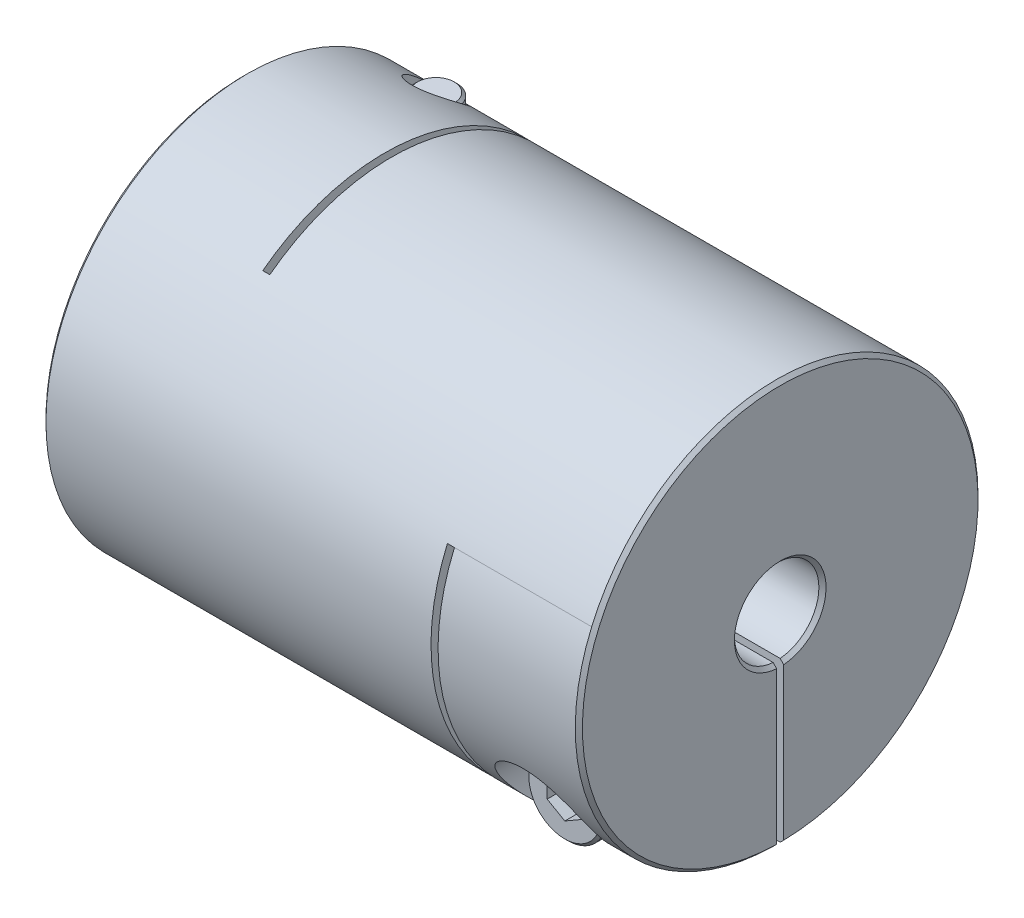
SolidWorks part; units mm, degrees
ref_plane "Front Plane" through (0, 0, 0) normal (0, 0, 1) x (1, 0, 0)
ref_plane "Top Plane" through (0, 0, 0) normal (0, 1, 0) x (1, 0, 0)
ref_plane "Right Plane" through (0, 0, 0) normal (1, 0, 0) x (0, 0, -1)
sketch "Sketch1" plane through (0, 0, 0) normal (1, 0, 0) x (0, 0, -1)
  circle A0 centre (0, 0) radius 14.3
  dimension "dim D" = 28.6
extrude "Boss-Extrude1" add sketch "Sketch1" along normal mid plane 38.1
sketch "Sketch2" plane through (19.05, 0, 0) normal (1, 0, 0) x (0, 0, -1)
  circle A0 centre (0, 0) radius 3
  dimension "dim D1" = 6
extrude "Cut-Extrude1" cut sketch "Sketch2" against normal through all
chamfer "Chamfer1" distance 0.254 angle 45 4 edges at (-19.05, 0, -3) (-19.05, 0, -14.3) (19.05, 0, -14.3) (19.05, 0, -3)
ref_plane "Plane2" through (0, -14.3, 0) normal (0, -1, 0) x (1, 0, 0)
ref_plane "L1" through (-14.05, 0, 0) normal (-1, 0, 0) x (0, 0, 1)
sketch "Sketch4" plane through (0, -14.3, 0) normal (0, -1, 0) x (1, 0, 0)
  line L0 (-18.796, -14.3) -> (18.796, -14.3) construction
  line L1 (-9.05, -14.3) -> (-8.55, -14.3)
  line L2 (-9.05, -14.3) -> (-9.05, 8.65)
  line L3 (-9.05, 8.65) -> (-8.55, 8.65)
  line L4 (-8.55, -14.3) -> (-8.55, 8.65)
  line L5 (-9.05, 3) -> (-9.05, 14.3) construction
  line L6 (18.796, 3) -> (-18.796, 3) construction
  line L7 (18.796, 14.3) -> (-18.796, 14.3) construction
  line L10 (-9.05, 8.65) -> (-19.05, 8.65) construction
  line L11 (-19.05, 14.046) -> (-19.05, -14.046) construction
  line L12 (-14.05, 10.2256) -> (-14.05, -10.2256) construction
  point P16 (-14.05, 8.65)
  dimension "D1" = 0.5
extrude "Cut-Extrude2" cut sketch "Sketch4" against normal through all
ref_plane "Plane4" through (0, 0, -14.3) normal (0, 0, -1) x (-1, 0, 0)
sketch "Sketch7" plane through (0, 0, -14.3) normal (0, 0, -1) x (-1, 0, 0)
  line L1 (-8.55, -14.3) -> (-9.05, -14.3)
  line L2 (-9.05, -14.3) -> (-9.05, 5.65)
  line L3 (-9.05, 5.65) -> (-8.55, 5.65)
  line L4 (-8.55, -14.3) -> (-8.55, 5.65)
  line L5 (19.05, 8.6487) -> (14.05, 8.6487) construction
  line L7 (-10.505, -14.3) -> (10.505, -14.3) construction
  line L8 (-18.796, -3) -> (8.55, -3) construction
  line L9 (19.05, -14.046) -> (19.05, 14.046) construction
  line L10 (-18.796, -3) -> (8.55, -3) construction
  line L11 (8.55, 11.3872) -> (9.05, 11.3872) construction
  line L12 (-9.05, 5.65) -> (-9.05, -14.3) construction
  line L14 (-18.796, -3) -> (8.55, -3) construction
  line L16 (-18.796, -3) -> (8.55, -3) construction
  line L17 (9.05, -14.3) -> (18.796, -14.3) construction
  line L18 (14.05, -10.2256) -> (14.05, 10.2256) construction
  line L19 (-18.796, -14.3) -> (-18.796, 14.3) construction
  line L20 (-19.05, 5.65) -> (-14.05, 5.65) construction
  line L21 (-19.05, 14.046) -> (-19.05, -14.046) construction
  line L22 (-14.05, 5.65) -> (-9.05, 5.65) construction
  line L23 (-18.796, -14.3) -> (-18.796, 14.3) construction
  line L24 (-18.796, -3) -> (-18.796, 14.3) construction
  line L25 (-18.796, -3) -> (8.55, -3) construction
  point P23 (-9.05, 5.65)
  point P33 (-18.796, 5.65)
extrude "Cut-Extrude3" cut sketch "Sketch7" against normal through all
sketch "Sketch8" plane through (0, 0, 0) normal (0, 1, 0) x (1, 0, 0)
  line L0 (-9.05, -8.65) -> (-9.05, 14.3) construction
  line L1 (-19.05, 14.3) -> (-9.05, 14.3)
  line L2 (-19.05, 14.3) -> (-19.05, 0)
  line L3 (-19.05, 0) -> (-9.05, 0)
  line L4 (-9.05, 14.3) -> (-9.05, 0)
  line L5 (10.505, 14.3) -> (-10.505, 14.3) construction
  line L6 (-19.05, 14.046) -> (-19.05, -14.046) construction
extrude "Cut-Extrude5" cut sketch "Sketch8" against normal mid plane 0.5
sketch "Sketch13" plane through (0, 0, 0) normal (0, 0, 1) x (1, 0, 0)
  line L0 (19.05, -14.046) -> (19.05, 14.046) construction
  line L1 (9.05, -14.3) -> (19.05, -14.3)
  line L2 (9.05, -14.3) -> (9.05, 0)
  line L3 (9.05, 0) -> (19.05, 0)
  line L4 (19.05, -14.3) -> (19.05, 0)
extrude "Cut-Extrude6" cut sketch "Sketch13" against normal mid plane 0.5
hole_wizard "CBORE for M3 SHCS1" positions "Sketch12" profile "Sketch11" counterbore size "M3" standard "Ansi Metric" end condition through all
sketch "Sketch12" plane through (0, -14.3, 0) normal (0, -1, 0) x (1, 0, 0)
  line L0 (-14.05, 10.2256) -> (-14.05, -10.2256) construction
  line L1 (-9.05, -2.9896) -> (-9.05, -14.2978) construction
  line L2 (-9.05, -2.9896) -> (-9.05, -14.2978)
  line L3 (-9.05, -8.6437) -> (-14.05, -8.6437) construction
  point P0 (-14.05, -8.6437)
sketch "Sketch11" plane through (-14.05, -14.3, -8.6437) normal (1, 0, 0) x (0, 0, -1)
  line L0 (0, 0) -> (0, 28.6)
  line L1 (0, 28.6) -> (1.7, 28.6)
  line L3 (1.7, 28.6) -> (1.7, 7)
  line L4 (1.7, 7) -> (3.25, 7)
  line L5 (3.25, 7) -> (3.25, 0)
  line L7 (3.25, 0) -> (0, 0)
  line L11 (0, -6.35) -> (0, 107.95) construction
  dimension "Thru Hole Dia." = 3.4
  dimension "Thru Hole Depth" = 28.6
  dimension "C'Bore Dia." = 6.5
  dimension "C'Bore Depth" = 7
ref_plane "Plane5" through (0, 0, 14.3) normal (0, 0, 1) x (1, 0, 0)
hole_wizard "CBORE for M3 SHCS2" positions "Sketch15" profile "Sketch14" counterbore size "M3" standard "Ansi Metric" end condition through all
sketch "Sketch15" plane through (0, 0, 14.3) normal (0, 0, 1) x (1, 0, 0)
  line L0 (-17.3, -7.3) -> (-10.8, -7.3) construction
  line L1 (-17.3, -7.3) -> (-10.8, -7.3)
  line L5 (0, 0) -> (0, 14.3) construction
  line L6 (-9.05, 14.3) -> (-18.796, 14.3) construction
  line L8 (17.3, -7.3) -> (10.8, -7.3)
  line L9 (14.05, -7.3) -> (14.05, -8.6437) construction
  line L11 (14.05, -14.2978) -> (14.05, -2.9896) construction
  line L12 (18.796, -14.2978) -> (9.05, -14.2978) construction
  line L13 (9.05, -2.9896) -> (18.796, -2.9896) construction
  point P0 (14.05, -8.6437)
sketch "Sketch14" plane through (14.05, -8.6437, 14.3) normal (1, 0, 0) x (0, -1, 0)
  line L0 (0, 0) -> (0, 28.6)
  line L1 (0, 28.6) -> (1.7, 28.6)
  line L3 (1.7, 28.6) -> (1.7, 7)
  line L4 (1.7, 7) -> (3.25, 7)
  line L5 (3.25, 7) -> (3.25, 0)
  line L7 (3.25, 0) -> (0, 0)
  line L11 (0, -6.35) -> (0, 107.95) construction
  dimension "Thru Hole Dia." = 3.4
  dimension "Thru Hole Depth" = 28.6
  dimension "C'Bore Dia." = 6.5
  dimension "C'Bore Depth" = 7
sketch "Sketch16" plane through (0, 0, 7.3) normal (0, 0, 1) x (1, 0, 0)
  circle A0 centre (14.05, -8.6437) radius 2.75
  dimension "screw dia" = 5.5
extrude "Boss-Extrude2" add sketch "Sketch16" along normal blind 3 separate body
sketch "Sketch17" plane through (0, 0, 7.3) normal (0, 0, -1) x (-1, 0, 0)
  circle A0 centre (-14.05, -8.6437) radius 1.5
  dimension "D1" = 3
extrude "Boss-Extrude3" add sketch "Sketch17" along normal blind 18.5
chamfer "Chamfer2" distance 0.2 angle 45 3 edges at (12.55, -8.6437, -11.2) (16.8, -8.6437, 7.3) (16.8, -8.6437, 10.3)
sketch "Sketch18" plane through (0, 0, 10.3) normal (0, 0, 1) x (1, 0, 0)
  line L1 (14.05, -10.0871) -> (15.3, -9.3654)
  line L2 (15.3, -9.3654) -> (15.3, -7.922)
  line L3 (15.3, -7.922) -> (14.05, -7.2003)
  line L4 (14.05, -7.2003) -> (12.8, -7.922)
  line L5 (12.8, -7.922) -> (12.8, -9.3654)
  line L6 (12.8, -9.3654) -> (14.05, -10.0871)
  circle A0 centre (14.05, -8.6437) radius 1.25 construction
  dimension "hex" = 2.5
extrude "Cut-Extrude7" cut sketch "Sketch18" against normal blind 1.5
mirror "Mirror1" about plane through (0, 0, 0) normal (1, 0, 0) of bodies 121
pattern_circular "CirPattern1" count 2 every 90 about axis through (0, 0, 0) along (1, 0, 0) of bodies 122
delete or keep bodies "Body-Delete1" type delete bodies bodies 122
